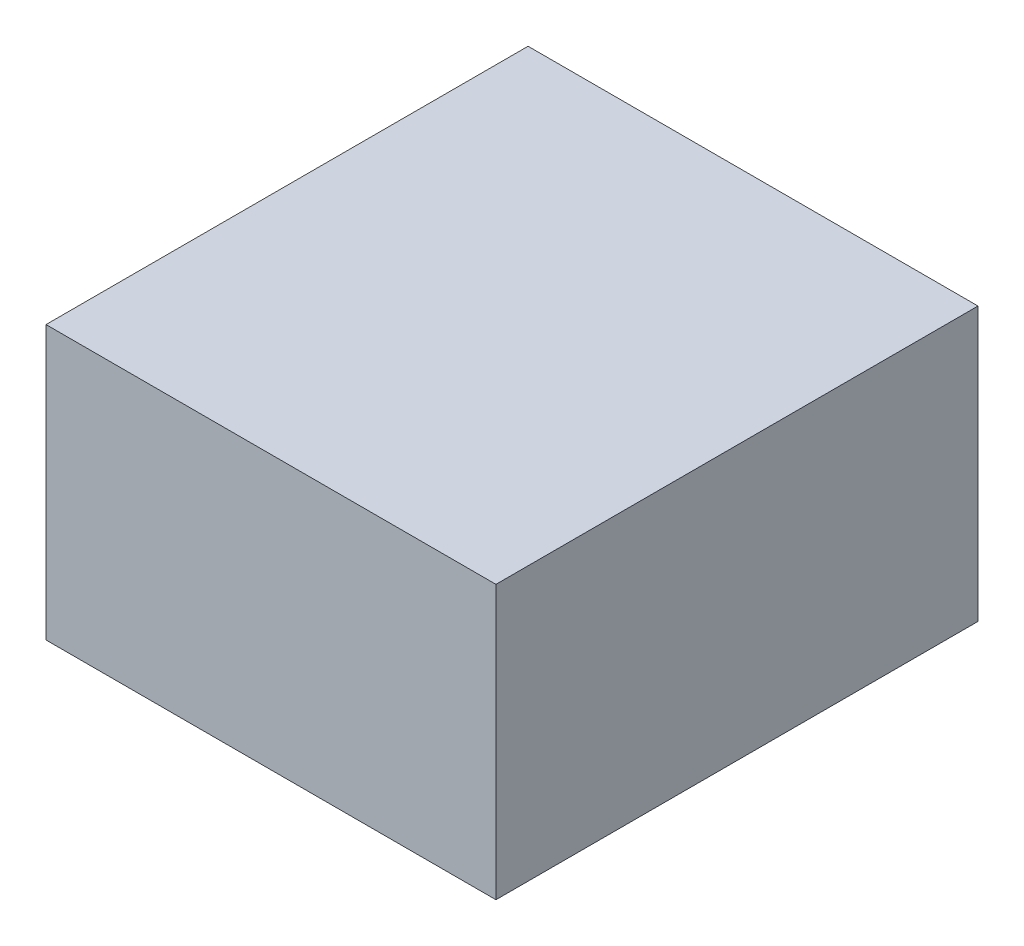
SolidWorks part; units mm, degrees
ref_plane "Front Plane" through (0, 0, 0) normal (0, 0, 1) x (1, 0, 0)
ref_plane "Top Plane" through (0, 0, 0) normal (0, 1, 0) x (1, 0, 0)
ref_plane "Right Plane" through (0, 0, 0) normal (1, 0, 0) x (0, 0, -1)
sketch "Sketch1" plane through (0, 0, 0) normal (0, 1, 0) x (1, 0, 0)
  line L1 (-70, 75) -> (70, 75)
  line L2 (-70, 75) -> (-70, -75)
  line L3 (-70, -75) -> (70, -75)
  line L4 (70, 75) -> (70, -75)
  line L5 (-70, 75) -> (70, -75) construction
  line L6 (-70, -75) -> (70, 75) construction
  point P0 (0, 0)
  dimension "D1" = 150
  dimension "D2" = 140
extrude "Boss-Extrude1" add sketch "Sketch1" along normal blind 85
sketch "Sketch2" plane through (-70, 0, 0) normal (-1, 0, 0) x (0, 0, 1)
  line L1 (23.5018, 55.6349) -> (50.423, 55.6349)
  line L2 (23.5018, 55.6349) -> (23.5018, 30.0164)
  line L3 (23.5018, 30.0164) -> (50.423, 30.0164)
  line L4 (50.423, 55.6349) -> (50.423, 30.0164)
  line L5 (23.5018, 55.6349) -> (50.423, 30.0164) construction
  line L6 (23.5018, 30.0164) -> (50.423, 55.6349) construction
  point P0 (36.9624, 42.8257)
extrude "Cut-Extrude1" cut sketch "Sketch2" against normal blind 20
sketch "Sketch3" plane through (-70, 0, 0) normal (-1, 0, 0) x (0, 0, 1)
  line L0 (-75, 85) -> (75, 85) construction
  line L1 (69, 79) -> (69, 85)
  line L2 (69, 79) -> (75, 79) construction
  line L3 (75, 85) -> (75, 0) construction
  line L4 (45, 6) -> (45, 0) construction
  line L5 (-75, 0) -> (75, 0) construction
  line L6 (45, 6) -> (75, 6) construction
  line L7 (-75, 85) -> (-75, 0) construction
  circle A0 centre (45, 6) radius 1.7525
  circle A1 centre (69, 79) radius 1.7525
  circle A2 centre (-69, 80) radius 1.7525
  circle A3 centre (-69, 16) radius 1.7525
  point P20 (-69, 16)
  point P21 (-69, 16)
  point P22 (-69, 80)
  point P23 (-69, 16)
  point P24 (0, 0)
  dimension "D7" = 3.505
  dimension "D1" = 6
  dimension "D2" = 30
  dimension "D3" = 6
  dimension "D4" = 6
  dimension "D5" = 5
  dimension "D6" = 16
extrude "Cut-Extrude2" cut sketch "Sketch3" against normal blind 10
